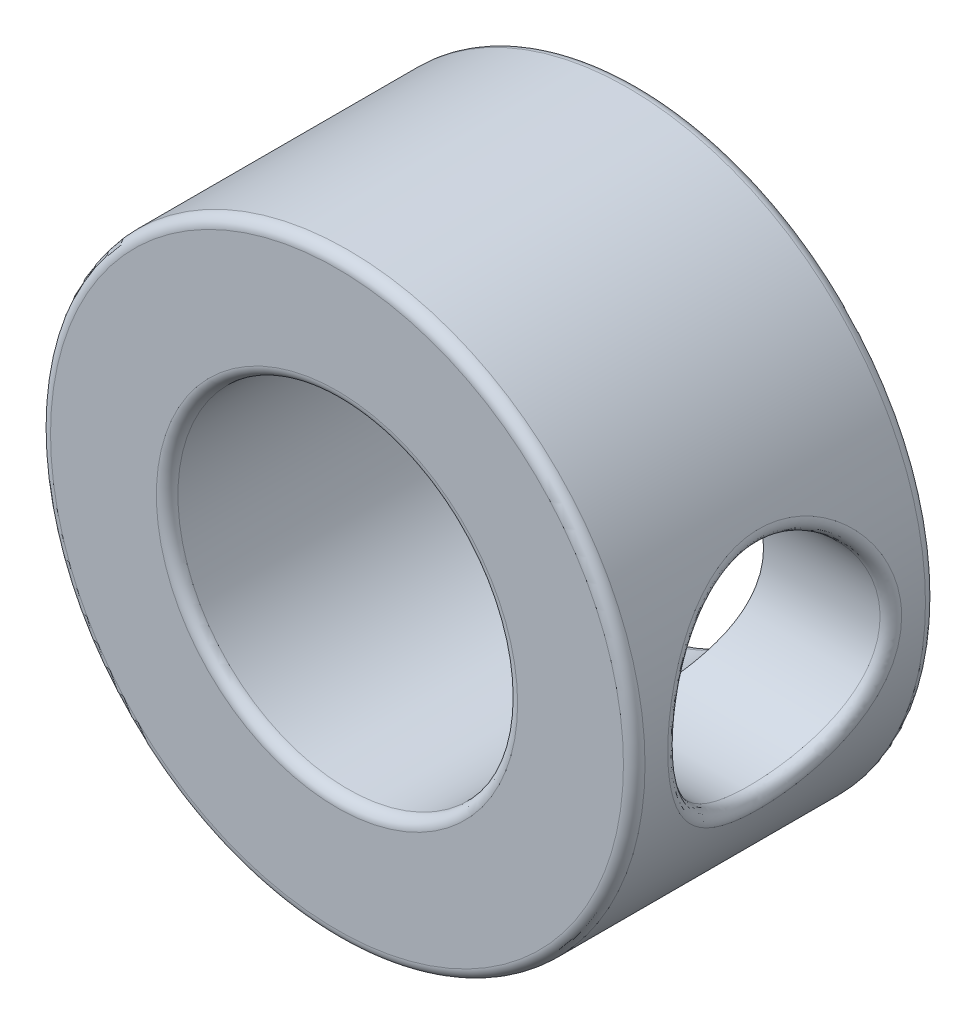
SolidWorks part; units mm, degrees
ref_plane "Front Plane" through (0, 0, 0) normal (0, 0, 1) x (1, 0, 0)
ref_plane "Top Plane" through (0, 0, 0) normal (0, 1, 0) x (1, 0, 0)
ref_plane "Right Plane" through (0, 0, 0) normal (1, 0, 0) x (0, 0, -1)
sketch "Sketch2" plane through (0, 0, 0) normal (0, 0, 1) x (1, 0, 0)
  circle A0 centre (0, 0) radius 7
  dimension "D1" = 14
extrude "Boss-Extrude1" add sketch "Sketch2" along normal blind 7.112
sketch "Sketch3" plane through (0, 0, 7.112) normal (0, 0, 1) x (1, 0, 0)
  circle A0 centre (0, 0) radius 4
  dimension "D1" = 8
extrude "Cut-Extrude1" cut sketch "Sketch3" against normal blind 19.05 contours A0
sketch "Sketch4" plane through (0, 0, 0) normal (1, 0, 0) x (0, 0, -1)
  circle A0 centre (-3.5687, 0) radius 2.5
  dimension "D1" = 5
  dimension "D2" = 3.5687
extrude "Cut-Extrude2" cut sketch "Sketch4" along normal blind 19.05
fillet "Fillet1" radius 0.254 5 edges at (4, 0, 0) (7, 0, 0) (6.9884, 0.4037, 1.1015) (4, 0, 7.112) (7, 0, 7.112)
